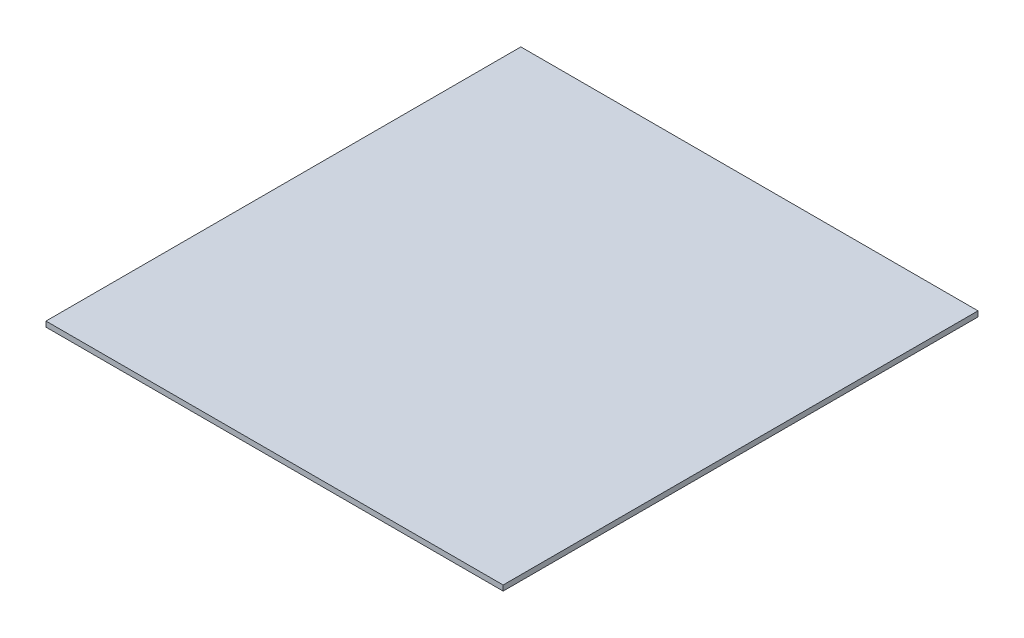
SolidWorks part; units mm, degrees
ref_plane "Front" through (0, 0, 0) normal (0, 0, 1) x (1, 0, 0)
ref_plane "Top" through (0, 0, 0) normal (0, 1, 0) x (1, 0, 0)
ref_plane "Right" through (0, 0, 0) normal (1, 0, 0) x (0, 0, -1)
sketch "Sketch1" plane through (0, 30, 0) normal (0, 1, 0) x (1, 0, 0)
  line L1 (0, 130) -> (125, 130)
  line L2 (0, 130) -> (0, 0)
  line L3 (0, 0) -> (125, 0)
  line L4 (125, 130) -> (125, 0)
  line L5 (0, 130) -> (125, 0) construction
  line L6 (0, 0) -> (125, 130) construction
  point P4 (62.5, 65)
extrude "Boss-Extrude1" add sketch "Sketch1" against normal blind 0.6
sketch "Sketch2" plane through (0, 30, 0) normal (0, 1, 0) x (1, 0, 0)
  line L1 (-2, -2) -> (127, -2)
  line L2 (-2, -2) -> (-2, 132)
  line L3 (-2, 132) -> (127, 132)
  line L4 (127, -2) -> (127, 132)
  line L5 (-2, -2) -> (127, 132) construction
  line L6 (-2, 132) -> (127, -2) construction
  point P4 (62.5, 65)
extrude "Boss-Extrude2" add sketch "Sketch2" along normal blind 1.5
